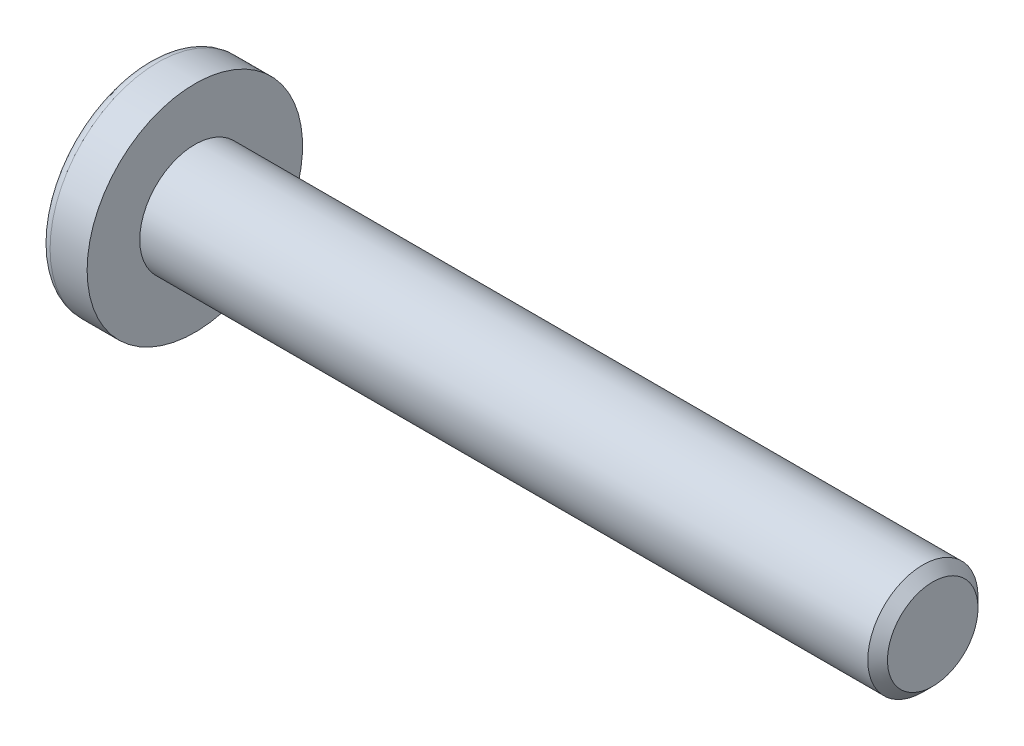
SolidWorks part; units mm, degrees
ref_plane "Plane1" through (0, 0, 0) normal (0, 0, 1) x (1, 0, 0)
ref_plane "Plane2" through (0, 0, 0) normal (0, 1, 0) x (1, 0, 0)
ref_plane "Plane3" through (0, 0, 0) normal (1, 0, 0) x (0, 0, -1)
sketch "BodySke" plane through (0, 0, 0) normal (0, 0, 1) x (1, 0, 0)
  line L0 (2.032, 1.4224) -> (2.032, 2.7813)
  line L1 (2.3495, 6.35) -> (2.3495, -3.175) construction
  line L2 (-25.4, 0) -> (127, 0) construction
  line L3 (21.082, 0) -> (0, 0)
  line L4 (2.032, 1.4224) -> (21.082, 1.4224)
  line L5 (21.082, 1.4224) -> (21.082, 0)
  line L6 (1.0756, 2.7813) -> (2.032, 2.7813)
  line L7 (2.032, -1.4224) -> (21.082, -1.4224) construction
  line L8 (2.032, 6.35) -> (2.032, -3.175) construction
  arc A0 (0.8702, 2.6767) -> (0, 0) centre (4.5517, 0) ccw
  arc A2 (0.8702, 2.6767) -> (1.0756, 2.7813) centre (1.0756, 2.5273) cw
  dimension "Head_fillet_rad" = 0.254
  dimension "Head_crown_rad" = 4.5517
  dimension "Head_ht" = 2.032
  dimension "Diameter" = 2.8448
  dimension "Length" = 19.05
  dimension "Head_dia" = 5.5626
  dimension "Advance" = 0.635
  dimension "Thread_nom" = 19.05
revolve "Base-Revolve" add sketch "BodySke" angle 360 about L2
cosmetic thread "ThreadCosmetic" [suppressed] parameters "Thread_length"=18.415, "Thread_minor"=2.0879
sketch "Sketch3" plane through (0, 0, 0) normal (1, 0, 0) x (0, 0, -1)
  line L0 (0.4064, -1.8161) -> (-0.4064, -1.8161)
  line L1 (0.4064, -1.8161) -> (0.4064, 1.8161)
  line L2 (-0.4064, 1.8161) -> (0.4064, 1.8161)
  line L3 (-0.4064, 1.8161) -> (-0.4064, -1.8161)
  dimension "D1" = 1.8161
  dimension "Cross_dia" = 3.6322
  dimension "D2" = 0.4064
  dimension "Cross_width" = 0.8128
ref_plane "Plane4" through (2.0066, 0, 0) normal (1, 0, 0) x (0, 0, -1)
sketch "Sketch4" plane through (2.0066, 0, 0) normal (1, 0, 0) x (0, 0, -1)
  line L0 (0.2032, -0.2032) -> (-0.2032, -0.2032)
  line L1 (0.2032, -0.2032) -> (0.2032, 0.2032)
  line L2 (-0.2032, 0.2032) -> (0.2032, 0.2032)
  line L3 (-0.2032, 0.2032) -> (-0.2032, -0.2032)
  dimension "D1" = 0.4064
  dimension "D2" = 0.4064
  dimension "D3" = 0.2032
  dimension "D4" = 0.2032
loft "Cut-Loft1" cut profiles "Sketch3", "Sketch4"
pattern_circular "CirPattern1" count 2 every 90 about axis through (0, 0, 0) along (1, 0, 0) of "Cut-Loft1"
sketch "ThdSchSke" plane through (0, 0, 0) normal (0, 0, 1) x (1, 0, 0)
  line L0 (2.667, -1.0439) -> (2.402, -1.4224)
  line L1 (2.667, -1.0439) -> (2.932, -1.4224)
  line L2 (2.932, -1.4224) -> (2.932, -1.778)
  line L3 (-3.175, 0) -> (5.1513, 0) construction
  line L5 (2.932, -1.778) -> (2.402, -1.778)
  line L6 (2.402, -1.778) -> (2.402, -1.4224)
  dimension "Thread_minor" = 2.0879
  dimension "Diameter" = 2.8448
  dimension "Start" = 2.667
  dimension "SideAngle" = 55
  dimension "VeeAngle" = 70
  dimension "Overcut" = 3.556
revolve "ThreadSchematic" [suppressed] cut sketch "ThdSchSke" angle 360 about L3
pattern_linear "ThdSchPat" [suppressed]
chamfer "Chamfer1" distance 0.254 angle 45 1 edges at (21.082, 0, 1.4224)
equation "\"D1@Sketch3\" = \"Cross_dia@Sketch3\" / 2"
equation "\"D2@Sketch3\" = \"Cross_width@Sketch3\" / 2"
equation "\"D1@Sketch4\" = \"Cross_width@Sketch3\" *.5"
equation "\"D2@Sketch4\" = \"D1@Sketch4\""
equation "\"D3@Sketch4\" = \"D1@Sketch4\" / 2"
equation "\"D4@Sketch4\" = \"D2@Sketch4\" / 2"
equation "\"Thread_length@ThreadCosmetic\" = ((sgn( (\"Length@BodySke\" - \"Advance@BodySke\" ) - \"Thread_nom@BodySke\" )-1)*( (\"Length@BodySke\" - \"Advance@BodySke\" ) - \"Thread_nom@BodySke\" ))/-2+ \"Thread_nom@BodySke\""
equation "\"Thread_minor@ThdSchSke\" = \"Thread_minor@ThreadCosmetic\""
equation "\"Diameter@ThdSchSke\" = \"Diameter@BodySke\""
equation "\"Overcut@ThdSchSke\" = \"Diameter@BodySke\" * 1.25"
equation "\"Start@ThdSchSke\" = \"Head_ht@BodySke\" + \"Length@BodySke\" - \"Thread_length@ThreadCosmetic\"  '---Non-countersunk---"
equation "\"Num_threads@ThdSchPat\" = int( \"Thread_length@ThreadCosmetic\" / \"Advance@BodySke\" + 0.999 )  + 1"
equation "\"Advance@ThdSchPat\" = \"Thread_length@ThreadCosmetic\" /  (\"Num_threads@ThdSchPat\" - 1) 'relax it"
